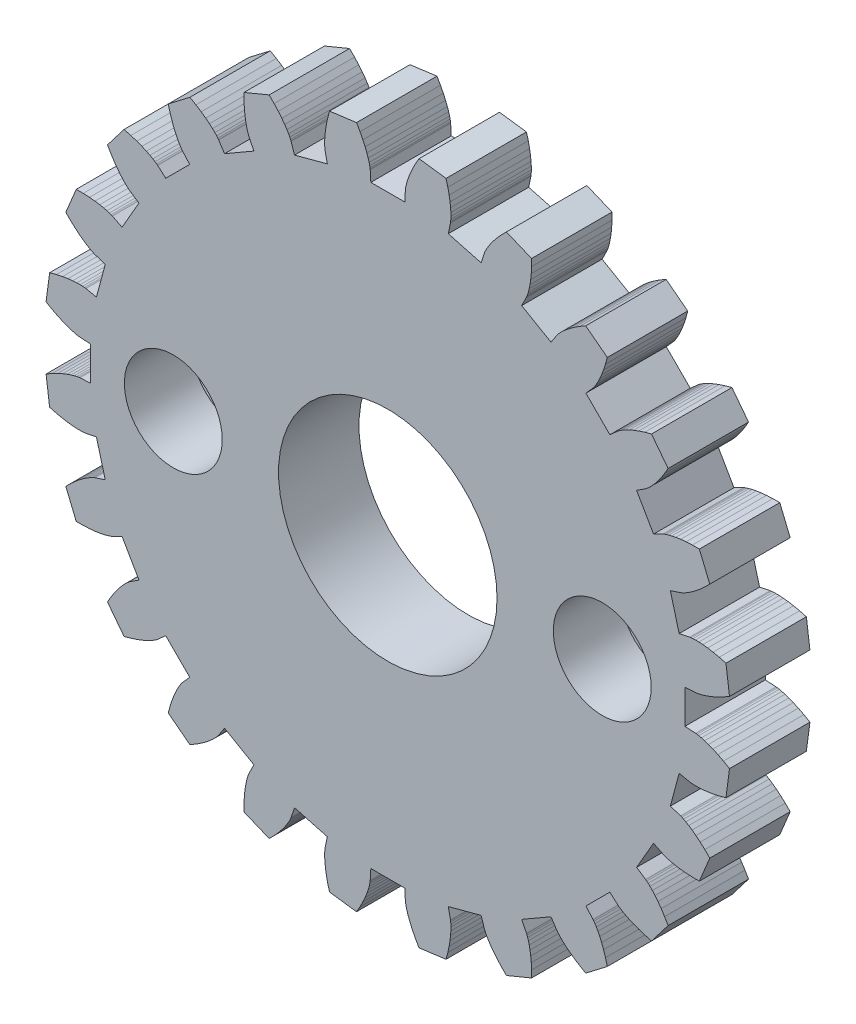
SolidWorks part; units mm, degrees
material "ABS"
ref_plane "Front Plane" through (0, 0, 0) normal (0, 0, 1) x (1, 0, 0)
ref_plane "Top Plane" through (0, 0, 0) normal (0, 1, 0) x (1, 0, 0)
ref_plane "Right Plane" through (0, 0, 0) normal (1, 0, 0) x (0, 0, -1)
sketch "Model" plane through (0, 0, 0) normal (0, 0, 1) x (1, 0, 0)
  line L0 (11.4813, -0.6559) -> (11.0819, -0.6331)
  line L1 (11.0819, -0.6331) -> (11.0819, 0.6331)
  line L2 (11.4813, 0.6559) -> (11.0819, 0.6331)
  line L3 (11.4813, 0.6559) -> (11.495, 0.6571)
  line L4 (11.495, 0.6571) -> (11.5358, 0.6626)
  line L5 (11.5358, 0.6626) -> (11.6033, 0.6749)
  line L6 (11.6033, 0.6749) -> (11.697, 0.6968)
  line L7 (11.697, 0.6968) -> (11.8158, 0.7307)
  line L8 (11.8158, 0.7307) -> (11.9589, 0.7792)
  line L9 (11.9589, 0.7792) -> (12.125, 0.8446)
  line L10 (12.125, 0.8446) -> (12.3128, 0.9294)
  line L11 (12.3128, 0.9294) -> (12.5206, 1.0358)
  line L12 (12.5206, 1.0358) -> (12.7468, 1.1658)
  line L13 (11.2598, 2.338) -> (11.2734, 2.3404)
  line L14 (11.2734, 2.3404) -> (11.3142, 2.3457)
  line L15 (11.3142, 2.3457) -> (11.3827, 2.3512)
  line L16 (11.3827, 2.3512) -> (11.4787, 2.3543)
  line L17 (11.4787, 2.3543) -> (11.6023, 2.3524)
  line L18 (11.6023, 2.3524) -> (11.7531, 2.3426)
  line L19 (11.7531, 2.3426) -> (11.9305, 2.3223)
  line L20 (11.9305, 2.3223) -> (12.1338, 2.289)
  line L21 (12.1338, 2.289) -> (12.362, 2.2401)
  line L22 (12.362, 2.2401) -> (12.6142, 2.173)
  line L23 (12.7468, 1.1658) -> (12.6142, 2.173)
  line L24 (11.2598, 2.338) -> (10.8682, 2.2567)
  line L25 (10.8682, 2.2567) -> (10.5405, 3.4797)
  line L26 (10.9203, 3.6051) -> (10.5405, 3.4797)
  line L27 (10.9203, 3.6051) -> (10.9332, 3.6098)
  line L28 (10.9332, 3.6098) -> (10.9712, 3.6257)
  line L29 (10.9712, 3.6257) -> (11.0333, 3.6551)
  line L30 (11.0333, 3.6551) -> (11.1181, 3.7004)
  line L31 (11.1181, 3.7004) -> (11.2241, 3.764)
  line L32 (11.2241, 3.764) -> (11.3497, 3.8478)
  line L33 (11.3497, 3.8478) -> (11.4933, 3.954)
  line L34 (11.4933, 3.954) -> (11.6527, 4.0845)
  line L35 (11.6527, 4.0845) -> (11.8259, 4.241)
  line L36 (11.8259, 4.241) -> (12.0107, 4.4252)
  line L37 (10.271, 5.1726) -> (10.2835, 5.1784)
  line L38 (10.2835, 5.1784) -> (10.3216, 5.1941)
  line L39 (10.3216, 5.1941) -> (10.3863, 5.2172)
  line L40 (10.3863, 5.2172) -> (10.4783, 5.245)
  line L41 (10.4783, 5.245) -> (10.5981, 5.2751)
  line L42 (10.5981, 5.2751) -> (10.7463, 5.3047)
  line L43 (10.7463, 5.3047) -> (10.9229, 5.331)
  line L44 (10.9229, 5.331) -> (11.1279, 5.3515)
  line L45 (11.1279, 5.3515) -> (11.361, 5.3633)
  line L46 (11.361, 5.3633) -> (11.622, 5.3638)
  line L47 (12.0107, 4.4252) -> (11.622, 5.3638)
  line L48 (10.271, 5.1726) -> (9.9138, 4.9927)
  line L49 (9.9138, 4.9927) -> (9.2807, 6.0892)
  line L50 (9.6151, 6.3087) -> (9.2807, 6.0892)
  line L51 (9.6151, 6.3087) -> (9.6264, 6.3166)
  line L52 (9.6264, 6.3166) -> (9.659, 6.3417)
  line L53 (9.659, 6.3417) -> (9.7113, 6.3862)
  line L54 (9.7113, 6.3862) -> (9.7815, 6.4519)
  line L55 (9.7815, 6.4519) -> (9.8675, 6.5407)
  line L56 (9.8675, 6.5407) -> (9.9671, 6.6542)
  line L57 (9.9671, 6.6542) -> (10.0783, 6.794)
  line L58 (10.0783, 6.794) -> (10.1985, 6.9613)
  line L59 (10.1985, 6.9613) -> (10.3253, 7.1573)
  line L60 (10.3253, 7.1573) -> (10.4561, 7.383)
  line L61 (8.5823, 7.6547) -> (8.5928, 7.6635)
  line L62 (8.5928, 7.6635) -> (8.6256, 7.6885)
  line L63 (8.6256, 7.6885) -> (8.6821, 7.7275)
  line L64 (8.6821, 7.7275) -> (8.7637, 7.7783)
  line L65 (8.7637, 7.7783) -> (8.8717, 7.8384)
  line L66 (8.8717, 7.8384) -> (9.0072, 7.9053)
  line L67 (9.0072, 7.9053) -> (9.1709, 7.9764)
  line L68 (9.1709, 7.9764) -> (9.3636, 8.0492)
  line L69 (9.3636, 8.0492) -> (9.5858, 8.121)
  line L70 (9.5858, 8.121) -> (9.8377, 8.189)
  line L71 (10.4561, 7.383) -> (9.8377, 8.189)
  line L72 (8.5823, 7.6547) -> (8.2838, 7.3885)
  line L73 (8.2838, 7.3885) -> (7.3885, 8.2838)
  line L74 (7.6547, 8.5823) -> (7.3885, 8.2838)
  line L75 (7.6547, 8.5823) -> (7.6635, 8.5928)
  line L76 (7.6635, 8.5928) -> (7.6885, 8.6256)
  line L77 (7.6885, 8.6256) -> (7.7275, 8.6821)
  line L78 (7.7275, 8.6821) -> (7.7783, 8.7637)
  line L79 (7.7783, 8.7637) -> (7.8384, 8.8717)
  line L80 (7.8384, 8.8717) -> (7.9053, 9.0072)
  line L81 (7.9053, 9.0072) -> (7.9764, 9.1709)
  line L82 (7.9764, 9.1709) -> (8.0492, 9.3636)
  line L83 (8.0492, 9.3636) -> (8.121, 9.5858)
  line L84 (8.121, 9.5858) -> (8.189, 9.8377)
  line L85 (6.3087, 9.6151) -> (6.3166, 9.6264)
  line L86 (6.3166, 9.6264) -> (6.3417, 9.659)
  line L87 (6.3417, 9.659) -> (6.3862, 9.7113)
  line L88 (6.3862, 9.7113) -> (6.4519, 9.7815)
  line L89 (6.4519, 9.7815) -> (6.5407, 9.8675)
  line L90 (6.5407, 9.8675) -> (6.6542, 9.9671)
  line L91 (6.6542, 9.9671) -> (6.794, 10.0783)
  line L92 (6.794, 10.0783) -> (6.9613, 10.1985)
  line L93 (6.9613, 10.1985) -> (7.1573, 10.3253)
  line L94 (7.1573, 10.3253) -> (7.383, 10.4561)
  line L95 (8.189, 9.8377) -> (7.383, 10.4561)
  line L96 (6.3087, 9.6151) -> (6.0892, 9.2807)
  line L97 (6.0892, 9.2807) -> (4.9927, 9.9138)
  line L98 (5.1726, 10.271) -> (4.9927, 9.9138)
  line L99 (5.1726, 10.271) -> (5.1784, 10.2835)
  line L100 (5.1784, 10.2835) -> (5.1941, 10.3216)
  line L101 (5.1941, 10.3216) -> (5.2172, 10.3863)
  line L102 (5.2172, 10.3863) -> (5.245, 10.4783)
  line L103 (5.245, 10.4783) -> (5.2751, 10.5981)
  line L104 (5.2751, 10.5981) -> (5.3047, 10.7463)
  line L105 (5.3047, 10.7463) -> (5.331, 10.9229)
  line L106 (5.331, 10.9229) -> (5.3515, 11.1279)
  line L107 (5.3515, 11.1279) -> (5.3633, 11.361)
  line L108 (5.3633, 11.361) -> (5.3638, 11.622)
  line L109 (3.6051, 10.9203) -> (3.6098, 10.9332)
  line L110 (3.6098, 10.9332) -> (3.6257, 10.9712)
  line L111 (3.6257, 10.9712) -> (3.6551, 11.0333)
  line L112 (3.6551, 11.0333) -> (3.7004, 11.1181)
  line L113 (3.7004, 11.1181) -> (3.764, 11.2241)
  line L114 (3.764, 11.2241) -> (3.8478, 11.3497)
  line L115 (3.8478, 11.3497) -> (3.954, 11.4933)
  line L116 (3.954, 11.4933) -> (4.0845, 11.6527)
  line L117 (4.0845, 11.6527) -> (4.241, 11.8259)
  line L118 (4.241, 11.8259) -> (4.4252, 12.0107)
  line L119 (5.3638, 11.622) -> (4.4252, 12.0107)
  line L120 (3.6051, 10.9203) -> (3.4797, 10.5405)
  line L121 (3.4797, 10.5405) -> (2.2567, 10.8682)
  line L122 (2.338, 11.2598) -> (2.2567, 10.8682)
  line L123 (2.338, 11.2598) -> (2.3404, 11.2734)
  line L124 (2.3404, 11.2734) -> (2.3457, 11.3142)
  line L125 (2.3457, 11.3142) -> (2.3512, 11.3827)
  line L126 (2.3512, 11.3827) -> (2.3543, 11.4787)
  line L127 (2.3543, 11.4787) -> (2.3524, 11.6023)
  line L128 (2.3524, 11.6023) -> (2.3426, 11.7531)
  line L129 (2.3426, 11.7531) -> (2.3223, 11.9305)
  line L130 (2.3223, 11.9305) -> (2.289, 12.1338)
  line L131 (2.289, 12.1338) -> (2.2401, 12.362)
  line L132 (2.2401, 12.362) -> (2.173, 12.6142)
  line L133 (0.6559, 11.4813) -> (0.6571, 11.495)
  line L134 (0.6571, 11.495) -> (0.6626, 11.5358)
  line L135 (0.6626, 11.5358) -> (0.6749, 11.6033)
  line L136 (0.6749, 11.6033) -> (0.6968, 11.697)
  line L137 (0.6968, 11.697) -> (0.7307, 11.8158)
  line L138 (0.7307, 11.8158) -> (0.7792, 11.9589)
  line L139 (0.7792, 11.9589) -> (0.8446, 12.125)
  line L140 (0.8446, 12.125) -> (0.9294, 12.3128)
  line L141 (0.9294, 12.3128) -> (1.0358, 12.5206)
  line L142 (1.0358, 12.5206) -> (1.1658, 12.7468)
  line L143 (2.173, 12.6142) -> (1.1658, 12.7468)
  line L144 (0.6559, 11.4813) -> (0.6331, 11.0819)
  line L145 (0.6331, 11.0819) -> (-0.6331, 11.0819)
  line L146 (-0.6559, 11.4813) -> (-0.6331, 11.0819)
  line L147 (-0.6559, 11.4813) -> (-0.6571, 11.495)
  line L148 (-0.6571, 11.495) -> (-0.6626, 11.5358)
  line L149 (-0.6626, 11.5358) -> (-0.6749, 11.6033)
  line L150 (-0.6749, 11.6033) -> (-0.6968, 11.697)
  line L151 (-0.6968, 11.697) -> (-0.7307, 11.8158)
  line L152 (-0.7307, 11.8158) -> (-0.7792, 11.9589)
  line L153 (-0.7792, 11.9589) -> (-0.8446, 12.125)
  line L154 (-0.8446, 12.125) -> (-0.9294, 12.3128)
  line L155 (-0.9294, 12.3128) -> (-1.0358, 12.5206)
  line L156 (-1.0358, 12.5206) -> (-1.1658, 12.7468)
  line L157 (-2.338, 11.2598) -> (-2.3404, 11.2734)
  line L158 (-2.3404, 11.2734) -> (-2.3457, 11.3142)
  line L159 (-2.3457, 11.3142) -> (-2.3512, 11.3827)
  line L160 (-2.3512, 11.3827) -> (-2.3543, 11.4787)
  line L161 (-2.3543, 11.4787) -> (-2.3524, 11.6023)
  line L162 (-2.3524, 11.6023) -> (-2.3426, 11.7531)
  line L163 (-2.3426, 11.7531) -> (-2.3223, 11.9305)
  line L164 (-2.3223, 11.9305) -> (-2.289, 12.1338)
  line L165 (-2.289, 12.1338) -> (-2.2401, 12.362)
  line L166 (-2.2401, 12.362) -> (-2.173, 12.6142)
  line L167 (-1.1658, 12.7468) -> (-2.173, 12.6142)
  line L168 (-2.338, 11.2598) -> (-2.2567, 10.8682)
  line L169 (-2.2567, 10.8682) -> (-3.4797, 10.5405)
  line L170 (-3.6051, 10.9203) -> (-3.4797, 10.5405)
  line L171 (-3.6051, 10.9203) -> (-3.6098, 10.9332)
  line L172 (-3.6098, 10.9332) -> (-3.6257, 10.9712)
  line L173 (-3.6257, 10.9712) -> (-3.6551, 11.0333)
  line L174 (-3.6551, 11.0333) -> (-3.7004, 11.1181)
  line L175 (-3.7004, 11.1181) -> (-3.764, 11.2241)
  line L176 (-3.764, 11.2241) -> (-3.8478, 11.3497)
  line L177 (-3.8478, 11.3497) -> (-3.954, 11.4933)
  line L178 (-3.954, 11.4933) -> (-4.0845, 11.6527)
  line L179 (-4.0845, 11.6527) -> (-4.241, 11.8259)
  line L180 (-4.241, 11.8259) -> (-4.4252, 12.0107)
  line L181 (-5.1726, 10.271) -> (-5.1784, 10.2835)
  line L182 (-5.1784, 10.2835) -> (-5.1941, 10.3216)
  line L183 (-5.1941, 10.3216) -> (-5.2172, 10.3863)
  line L184 (-5.2172, 10.3863) -> (-5.245, 10.4783)
  line L185 (-5.245, 10.4783) -> (-5.2751, 10.5981)
  line L186 (-5.2751, 10.5981) -> (-5.3047, 10.7463)
  line L187 (-5.3047, 10.7463) -> (-5.331, 10.9229)
  line L188 (-5.331, 10.9229) -> (-5.3515, 11.1279)
  line L189 (-5.3515, 11.1279) -> (-5.3633, 11.361)
  line L190 (-5.3633, 11.361) -> (-5.3638, 11.622)
  line L191 (-4.4252, 12.0107) -> (-5.3638, 11.622)
  line L192 (-5.1726, 10.271) -> (-4.9927, 9.9138)
  line L193 (-4.9927, 9.9138) -> (-6.0892, 9.2807)
  line L194 (-6.3087, 9.6151) -> (-6.0892, 9.2807)
  line L195 (-6.3087, 9.6151) -> (-6.3166, 9.6264)
  line L196 (-6.3166, 9.6264) -> (-6.3417, 9.659)
  line L197 (-6.3417, 9.659) -> (-6.3862, 9.7113)
  line L198 (-6.3862, 9.7113) -> (-6.4519, 9.7815)
  line L199 (-6.4519, 9.7815) -> (-6.5407, 9.8675)
  line L200 (-6.5407, 9.8675) -> (-6.6542, 9.9671)
  line L201 (-6.6542, 9.9671) -> (-6.794, 10.0783)
  line L202 (-6.794, 10.0783) -> (-6.9613, 10.1985)
  line L203 (-6.9613, 10.1985) -> (-7.1573, 10.3253)
  line L204 (-7.1573, 10.3253) -> (-7.383, 10.4561)
  line L205 (-7.6547, 8.5823) -> (-7.6635, 8.5928)
  line L206 (-7.6635, 8.5928) -> (-7.6885, 8.6256)
  line L207 (-7.6885, 8.6256) -> (-7.7275, 8.6821)
  line L208 (-7.7275, 8.6821) -> (-7.7783, 8.7637)
  line L209 (-7.7783, 8.7637) -> (-7.8384, 8.8717)
  line L210 (-7.8384, 8.8717) -> (-7.9053, 9.0072)
  line L211 (-7.9053, 9.0072) -> (-7.9764, 9.1709)
  line L212 (-7.9764, 9.1709) -> (-8.0492, 9.3636)
  line L213 (-8.0492, 9.3636) -> (-8.121, 9.5858)
  line L214 (-8.121, 9.5858) -> (-8.189, 9.8377)
  line L215 (-7.383, 10.4561) -> (-8.189, 9.8377)
  line L216 (-7.6547, 8.5823) -> (-7.3885, 8.2838)
  line L217 (-7.3885, 8.2838) -> (-8.2838, 7.3885)
  line L218 (-8.5823, 7.6547) -> (-8.2838, 7.3885)
  line L219 (-8.5823, 7.6547) -> (-8.5928, 7.6635)
  line L220 (-8.5928, 7.6635) -> (-8.6256, 7.6885)
  line L221 (-8.6256, 7.6885) -> (-8.6821, 7.7275)
  line L222 (-8.6821, 7.7275) -> (-8.7637, 7.7783)
  line L223 (-8.7637, 7.7783) -> (-8.8717, 7.8384)
  line L224 (-8.8717, 7.8384) -> (-9.0072, 7.9053)
  line L225 (-9.0072, 7.9053) -> (-9.1709, 7.9764)
  line L226 (-9.1709, 7.9764) -> (-9.3636, 8.0492)
  line L227 (-9.3636, 8.0492) -> (-9.5858, 8.121)
  line L228 (-9.5858, 8.121) -> (-9.8377, 8.189)
  line L229 (-9.6151, 6.3087) -> (-9.6264, 6.3166)
  line L230 (-9.6264, 6.3166) -> (-9.659, 6.3417)
  line L231 (-9.659, 6.3417) -> (-9.7113, 6.3862)
  line L232 (-9.7113, 6.3862) -> (-9.7815, 6.4519)
  line L233 (-9.7815, 6.4519) -> (-9.8675, 6.5407)
  line L234 (-9.8675, 6.5407) -> (-9.9671, 6.6542)
  line L235 (-9.9671, 6.6542) -> (-10.0783, 6.794)
  line L236 (-10.0783, 6.794) -> (-10.1985, 6.9613)
  line L237 (-10.1985, 6.9613) -> (-10.3253, 7.1573)
  line L238 (-10.3253, 7.1573) -> (-10.4561, 7.383)
  line L239 (-9.8377, 8.189) -> (-10.4561, 7.383)
  line L240 (-9.6151, 6.3087) -> (-9.2807, 6.0892)
  line L241 (-9.2807, 6.0892) -> (-9.9138, 4.9927)
  line L242 (-10.271, 5.1726) -> (-9.9138, 4.9927)
  line L243 (-10.271, 5.1726) -> (-10.2835, 5.1784)
  line L244 (-10.2835, 5.1784) -> (-10.3216, 5.1941)
  line L245 (-10.3216, 5.1941) -> (-10.3863, 5.2172)
  line L246 (-10.3863, 5.2172) -> (-10.4783, 5.245)
  line L247 (-10.4783, 5.245) -> (-10.5981, 5.2751)
  line L248 (-10.5981, 5.2751) -> (-10.7463, 5.3047)
  line L249 (-10.7463, 5.3047) -> (-10.9229, 5.331)
  line L250 (-10.9229, 5.331) -> (-11.1279, 5.3515)
  line L251 (-11.1279, 5.3515) -> (-11.361, 5.3633)
  line L252 (-11.361, 5.3633) -> (-11.622, 5.3638)
  line L253 (-10.9203, 3.6051) -> (-10.9332, 3.6098)
  line L254 (-10.9332, 3.6098) -> (-10.9712, 3.6257)
  line L255 (-10.9712, 3.6257) -> (-11.0333, 3.6551)
  line L256 (-11.0333, 3.6551) -> (-11.1181, 3.7004)
  line L257 (-11.1181, 3.7004) -> (-11.2241, 3.764)
  line L258 (-11.2241, 3.764) -> (-11.3497, 3.8478)
  line L259 (-11.3497, 3.8478) -> (-11.4933, 3.954)
  line L260 (-11.4933, 3.954) -> (-11.6527, 4.0845)
  line L261 (-11.6527, 4.0845) -> (-11.8259, 4.241)
  line L262 (-11.8259, 4.241) -> (-12.0107, 4.4252)
  line L263 (-11.622, 5.3638) -> (-12.0107, 4.4252)
  line L264 (-10.9203, 3.6051) -> (-10.5405, 3.4797)
  line L265 (-10.5405, 3.4797) -> (-10.8682, 2.2567)
  line L266 (-11.2598, 2.338) -> (-10.8682, 2.2567)
  line L267 (-11.2598, 2.338) -> (-11.2734, 2.3404)
  line L268 (-11.2734, 2.3404) -> (-11.3142, 2.3457)
  line L269 (-11.3142, 2.3457) -> (-11.3827, 2.3512)
  line L270 (-11.3827, 2.3512) -> (-11.4787, 2.3543)
  line L271 (-11.4787, 2.3543) -> (-11.6023, 2.3524)
  line L272 (-11.6023, 2.3524) -> (-11.7531, 2.3426)
  line L273 (-11.7531, 2.3426) -> (-11.9305, 2.3223)
  line L274 (-11.9305, 2.3223) -> (-12.1338, 2.289)
  line L275 (-12.1338, 2.289) -> (-12.362, 2.2401)
  line L276 (-12.362, 2.2401) -> (-12.6142, 2.173)
  line L277 (-11.4813, 0.6559) -> (-11.495, 0.6571)
  line L278 (-11.495, 0.6571) -> (-11.5358, 0.6626)
  line L279 (-11.5358, 0.6626) -> (-11.6033, 0.6749)
  line L280 (-11.6033, 0.6749) -> (-11.697, 0.6968)
  line L281 (-11.697, 0.6968) -> (-11.8158, 0.7307)
  line L282 (-11.8158, 0.7307) -> (-11.9589, 0.7792)
  line L283 (-11.9589, 0.7792) -> (-12.125, 0.8446)
  line L284 (-12.125, 0.8446) -> (-12.3128, 0.9294)
  line L285 (-12.3128, 0.9294) -> (-12.5206, 1.0358)
  line L286 (-12.5206, 1.0358) -> (-12.7468, 1.1658)
  line L287 (-12.6142, 2.173) -> (-12.7468, 1.1658)
  line L288 (-11.4813, 0.6559) -> (-11.0819, 0.6331)
  line L289 (-11.0819, 0.6331) -> (-11.0819, -0.6331)
  line L290 (-11.4813, -0.6559) -> (-11.0819, -0.6331)
  line L291 (-11.4813, -0.6559) -> (-11.495, -0.6571)
  line L292 (-11.495, -0.6571) -> (-11.5358, -0.6626)
  line L293 (-11.5358, -0.6626) -> (-11.6033, -0.6749)
  line L294 (-11.6033, -0.6749) -> (-11.697, -0.6968)
  line L295 (-11.697, -0.6968) -> (-11.8158, -0.7307)
  line L296 (-11.8158, -0.7307) -> (-11.9589, -0.7792)
  line L297 (-11.9589, -0.7792) -> (-12.125, -0.8446)
  line L298 (-12.125, -0.8446) -> (-12.3128, -0.9294)
  line L299 (-12.3128, -0.9294) -> (-12.5206, -1.0358)
  line L300 (-12.5206, -1.0358) -> (-12.7468, -1.1658)
  line L301 (-11.2598, -2.338) -> (-11.2734, -2.3404)
  line L302 (-11.2734, -2.3404) -> (-11.3142, -2.3457)
  line L303 (-11.3142, -2.3457) -> (-11.3827, -2.3512)
  line L304 (-11.3827, -2.3512) -> (-11.4787, -2.3543)
  line L305 (-11.4787, -2.3543) -> (-11.6023, -2.3524)
  line L306 (-11.6023, -2.3524) -> (-11.7531, -2.3426)
  line L307 (-11.7531, -2.3426) -> (-11.9305, -2.3223)
  line L308 (-11.9305, -2.3223) -> (-12.1338, -2.289)
  line L309 (-12.1338, -2.289) -> (-12.362, -2.2401)
  line L310 (-12.362, -2.2401) -> (-12.6142, -2.173)
  line L311 (-12.7468, -1.1658) -> (-12.6142, -2.173)
  line L312 (-11.2598, -2.338) -> (-10.8682, -2.2567)
  line L313 (-10.8682, -2.2567) -> (-10.5405, -3.4797)
  line L314 (-10.9203, -3.6051) -> (-10.5405, -3.4797)
  line L315 (-10.9203, -3.6051) -> (-10.9332, -3.6098)
  line L316 (-10.9332, -3.6098) -> (-10.9712, -3.6257)
  line L317 (-10.9712, -3.6257) -> (-11.0333, -3.6551)
  line L318 (-11.0333, -3.6551) -> (-11.1181, -3.7004)
  line L319 (-11.1181, -3.7004) -> (-11.2241, -3.764)
  line L320 (-11.2241, -3.764) -> (-11.3497, -3.8478)
  line L321 (-11.3497, -3.8478) -> (-11.4933, -3.954)
  line L322 (-11.4933, -3.954) -> (-11.6527, -4.0845)
  line L323 (-11.6527, -4.0845) -> (-11.8259, -4.241)
  line L324 (-11.8259, -4.241) -> (-12.0107, -4.4252)
  line L325 (-10.271, -5.1726) -> (-10.2835, -5.1784)
  line L326 (-10.2835, -5.1784) -> (-10.3216, -5.1941)
  line L327 (-10.3216, -5.1941) -> (-10.3863, -5.2172)
  line L328 (-10.3863, -5.2172) -> (-10.4783, -5.245)
  line L329 (-10.4783, -5.245) -> (-10.5981, -5.2751)
  line L330 (-10.5981, -5.2751) -> (-10.7463, -5.3047)
  line L331 (-10.7463, -5.3047) -> (-10.9229, -5.331)
  line L332 (-10.9229, -5.331) -> (-11.1279, -5.3515)
  line L333 (-11.1279, -5.3515) -> (-11.361, -5.3633)
  line L334 (-11.361, -5.3633) -> (-11.622, -5.3638)
  line L335 (-12.0107, -4.4252) -> (-11.622, -5.3638)
  line L336 (-10.271, -5.1726) -> (-9.9138, -4.9927)
  line L337 (-9.9138, -4.9927) -> (-9.2807, -6.0892)
  line L338 (-9.6151, -6.3087) -> (-9.2807, -6.0892)
  line L339 (-9.6151, -6.3087) -> (-9.6264, -6.3166)
  line L340 (-9.6264, -6.3166) -> (-9.659, -6.3417)
  line L341 (-9.659, -6.3417) -> (-9.7113, -6.3862)
  line L342 (-9.7113, -6.3862) -> (-9.7815, -6.4519)
  line L343 (-9.7815, -6.4519) -> (-9.8675, -6.5407)
  line L344 (-9.8675, -6.5407) -> (-9.9671, -6.6542)
  line L345 (-9.9671, -6.6542) -> (-10.0783, -6.794)
  line L346 (-10.0783, -6.794) -> (-10.1985, -6.9613)
  line L347 (-10.1985, -6.9613) -> (-10.3253, -7.1573)
  line L348 (-10.3253, -7.1573) -> (-10.4561, -7.383)
  line L349 (-8.5823, -7.6547) -> (-8.5928, -7.6635)
  line L350 (-8.5928, -7.6635) -> (-8.6256, -7.6885)
  line L351 (-8.6256, -7.6885) -> (-8.6821, -7.7275)
  line L352 (-8.6821, -7.7275) -> (-8.7637, -7.7783)
  line L353 (-8.7637, -7.7783) -> (-8.8717, -7.8384)
  line L354 (-8.8717, -7.8384) -> (-9.0072, -7.9053)
  line L355 (-9.0072, -7.9053) -> (-9.1709, -7.9764)
  line L356 (-9.1709, -7.9764) -> (-9.3636, -8.0492)
  line L357 (-9.3636, -8.0492) -> (-9.5858, -8.121)
  line L358 (-9.5858, -8.121) -> (-9.8377, -8.189)
  line L359 (-10.4561, -7.383) -> (-9.8377, -8.189)
  line L360 (-8.5823, -7.6547) -> (-8.2838, -7.3885)
  line L361 (-8.2838, -7.3885) -> (-7.3885, -8.2838)
  line L362 (-7.6547, -8.5823) -> (-7.3885, -8.2838)
  line L363 (-7.6547, -8.5823) -> (-7.6635, -8.5928)
  line L364 (-7.6635, -8.5928) -> (-7.6885, -8.6256)
  line L365 (-7.6885, -8.6256) -> (-7.7275, -8.6821)
  line L366 (-7.7275, -8.6821) -> (-7.7783, -8.7637)
  line L367 (-7.7783, -8.7637) -> (-7.8384, -8.8717)
  line L368 (-7.8384, -8.8717) -> (-7.9053, -9.0072)
  line L369 (-7.9053, -9.0072) -> (-7.9764, -9.1709)
  line L370 (-7.9764, -9.1709) -> (-8.0492, -9.3636)
  line L371 (-8.0492, -9.3636) -> (-8.121, -9.5858)
  line L372 (-8.121, -9.5858) -> (-8.189, -9.8377)
  line L373 (-6.3087, -9.6151) -> (-6.3166, -9.6264)
  line L374 (-6.3166, -9.6264) -> (-6.3417, -9.659)
  line L375 (-6.3417, -9.659) -> (-6.3862, -9.7113)
  line L376 (-6.3862, -9.7113) -> (-6.4519, -9.7815)
  line L377 (-6.4519, -9.7815) -> (-6.5407, -9.8675)
  line L378 (-6.5407, -9.8675) -> (-6.6542, -9.9671)
  line L379 (-6.6542, -9.9671) -> (-6.794, -10.0783)
  line L380 (-6.794, -10.0783) -> (-6.9613, -10.1985)
  line L381 (-6.9613, -10.1985) -> (-7.1573, -10.3253)
  line L382 (-7.1573, -10.3253) -> (-7.383, -10.4561)
  line L383 (-8.189, -9.8377) -> (-7.383, -10.4561)
  line L384 (-6.3087, -9.6151) -> (-6.0892, -9.2807)
  line L385 (-6.0892, -9.2807) -> (-4.9927, -9.9138)
  line L386 (-5.1726, -10.271) -> (-4.9927, -9.9138)
  line L387 (-5.1726, -10.271) -> (-5.1784, -10.2835)
  line L388 (-5.1784, -10.2835) -> (-5.1941, -10.3216)
  line L389 (-5.1941, -10.3216) -> (-5.2172, -10.3863)
  line L390 (-5.2172, -10.3863) -> (-5.245, -10.4783)
  line L391 (-5.245, -10.4783) -> (-5.2751, -10.5981)
  line L392 (-5.2751, -10.5981) -> (-5.3047, -10.7463)
  line L393 (-5.3047, -10.7463) -> (-5.331, -10.9229)
  line L394 (-5.331, -10.9229) -> (-5.3515, -11.1279)
  line L395 (-5.3515, -11.1279) -> (-5.3633, -11.361)
  line L396 (-5.3633, -11.361) -> (-5.3638, -11.622)
  line L397 (-3.6051, -10.9203) -> (-3.6098, -10.9332)
  line L398 (-3.6098, -10.9332) -> (-3.6257, -10.9712)
  line L399 (-3.6257, -10.9712) -> (-3.6551, -11.0333)
  line L400 (-3.6551, -11.0333) -> (-3.7004, -11.1181)
  line L401 (-3.7004, -11.1181) -> (-3.764, -11.2241)
  line L402 (-3.764, -11.2241) -> (-3.8478, -11.3497)
  line L403 (-3.8478, -11.3497) -> (-3.954, -11.4933)
  line L404 (-3.954, -11.4933) -> (-4.0845, -11.6527)
  line L405 (-4.0845, -11.6527) -> (-4.241, -11.8259)
  line L406 (-4.241, -11.8259) -> (-4.4252, -12.0107)
  line L407 (-5.3638, -11.622) -> (-4.4252, -12.0107)
  line L408 (-3.6051, -10.9203) -> (-3.4797, -10.5405)
  line L409 (-3.4797, -10.5405) -> (-2.2567, -10.8682)
  line L410 (-2.338, -11.2598) -> (-2.2567, -10.8682)
  line L411 (-2.338, -11.2598) -> (-2.3404, -11.2734)
  line L412 (-2.3404, -11.2734) -> (-2.3457, -11.3142)
  line L413 (-2.3457, -11.3142) -> (-2.3512, -11.3827)
  line L414 (-2.3512, -11.3827) -> (-2.3543, -11.4787)
  line L415 (-2.3543, -11.4787) -> (-2.3524, -11.6023)
  line L416 (-2.3524, -11.6023) -> (-2.3426, -11.7531)
  line L417 (-2.3426, -11.7531) -> (-2.3223, -11.9305)
  line L418 (-2.3223, -11.9305) -> (-2.289, -12.1338)
  line L419 (-2.289, -12.1338) -> (-2.2401, -12.362)
  line L420 (-2.2401, -12.362) -> (-2.173, -12.6142)
  line L421 (-0.6559, -11.4813) -> (-0.6571, -11.495)
  line L422 (-0.6571, -11.495) -> (-0.6626, -11.5358)
  line L423 (-0.6626, -11.5358) -> (-0.6749, -11.6033)
  line L424 (-0.6749, -11.6033) -> (-0.6968, -11.697)
  line L425 (-0.6968, -11.697) -> (-0.7307, -11.8158)
  line L426 (-0.7307, -11.8158) -> (-0.7792, -11.9589)
  line L427 (-0.7792, -11.9589) -> (-0.8446, -12.125)
  line L428 (-0.8446, -12.125) -> (-0.9294, -12.3128)
  line L429 (-0.9294, -12.3128) -> (-1.0358, -12.5206)
  line L430 (-1.0358, -12.5206) -> (-1.1658, -12.7468)
  line L431 (-2.173, -12.6142) -> (-1.1658, -12.7468)
  line L432 (-0.6559, -11.4813) -> (-0.6331, -11.0819)
  line L433 (-0.6331, -11.0819) -> (0.6331, -11.0819)
  line L434 (0.6559, -11.4813) -> (0.6331, -11.0819)
  line L435 (0.6559, -11.4813) -> (0.6571, -11.495)
  line L436 (0.6571, -11.495) -> (0.6626, -11.5358)
  line L437 (0.6626, -11.5358) -> (0.6749, -11.6033)
  line L438 (0.6749, -11.6033) -> (0.6968, -11.697)
  line L439 (0.6968, -11.697) -> (0.7307, -11.8158)
  line L440 (0.7307, -11.8158) -> (0.7792, -11.9589)
  line L441 (0.7792, -11.9589) -> (0.8446, -12.125)
  line L442 (0.8446, -12.125) -> (0.9294, -12.3128)
  line L443 (0.9294, -12.3128) -> (1.0358, -12.5206)
  line L444 (1.0358, -12.5206) -> (1.1658, -12.7468)
  line L445 (2.338, -11.2598) -> (2.3404, -11.2734)
  line L446 (2.3404, -11.2734) -> (2.3457, -11.3142)
  line L447 (2.3457, -11.3142) -> (2.3512, -11.3827)
  line L448 (2.3512, -11.3827) -> (2.3543, -11.4787)
  line L449 (2.3543, -11.4787) -> (2.3524, -11.6023)
  line L450 (2.3524, -11.6023) -> (2.3426, -11.7531)
  line L451 (2.3426, -11.7531) -> (2.3223, -11.9305)
  line L452 (2.3223, -11.9305) -> (2.289, -12.1338)
  line L453 (2.289, -12.1338) -> (2.2401, -12.362)
  line L454 (2.2401, -12.362) -> (2.173, -12.6142)
  line L455 (1.1658, -12.7468) -> (2.173, -12.6142)
  line L456 (2.338, -11.2598) -> (2.2567, -10.8682)
  line L457 (2.2567, -10.8682) -> (3.4797, -10.5405)
  line L458 (3.6051, -10.9203) -> (3.4797, -10.5405)
  line L459 (3.6051, -10.9203) -> (3.6098, -10.9332)
  line L460 (3.6098, -10.9332) -> (3.6257, -10.9712)
  line L461 (3.6257, -10.9712) -> (3.6551, -11.0333)
  line L462 (3.6551, -11.0333) -> (3.7004, -11.1181)
  line L463 (3.7004, -11.1181) -> (3.764, -11.2241)
  line L464 (3.764, -11.2241) -> (3.8478, -11.3497)
  line L465 (3.8478, -11.3497) -> (3.954, -11.4933)
  line L466 (3.954, -11.4933) -> (4.0845, -11.6527)
  line L467 (4.0845, -11.6527) -> (4.241, -11.8259)
  line L468 (4.241, -11.8259) -> (4.4252, -12.0107)
  line L469 (5.1726, -10.271) -> (5.1784, -10.2835)
  line L470 (5.1784, -10.2835) -> (5.1941, -10.3216)
  line L471 (5.1941, -10.3216) -> (5.2172, -10.3863)
  line L472 (5.2172, -10.3863) -> (5.245, -10.4783)
  line L473 (5.245, -10.4783) -> (5.2751, -10.5981)
  line L474 (5.2751, -10.5981) -> (5.3047, -10.7463)
  line L475 (5.3047, -10.7463) -> (5.331, -10.9229)
  line L476 (5.331, -10.9229) -> (5.3515, -11.1279)
  line L477 (5.3515, -11.1279) -> (5.3633, -11.361)
  line L478 (5.3633, -11.361) -> (5.3638, -11.622)
  line L479 (4.4252, -12.0107) -> (5.3638, -11.622)
  line L480 (5.1726, -10.271) -> (4.9927, -9.9138)
  line L481 (4.9927, -9.9138) -> (6.0892, -9.2807)
  line L482 (6.3087, -9.6151) -> (6.0892, -9.2807)
  line L483 (6.3087, -9.6151) -> (6.3166, -9.6264)
  line L484 (6.3166, -9.6264) -> (6.3417, -9.659)
  line L485 (6.3417, -9.659) -> (6.3862, -9.7113)
  line L486 (6.3862, -9.7113) -> (6.4519, -9.7815)
  line L487 (6.4519, -9.7815) -> (6.5407, -9.8675)
  line L488 (6.5407, -9.8675) -> (6.6542, -9.9671)
  line L489 (6.6542, -9.9671) -> (6.794, -10.0783)
  line L490 (6.794, -10.0783) -> (6.9613, -10.1985)
  line L491 (6.9613, -10.1985) -> (7.1573, -10.3253)
  line L492 (7.1573, -10.3253) -> (7.383, -10.4561)
  line L493 (7.6547, -8.5823) -> (7.6635, -8.5928)
  line L494 (7.6635, -8.5928) -> (7.6885, -8.6256)
  line L495 (7.6885, -8.6256) -> (7.7275, -8.6821)
  line L496 (7.7275, -8.6821) -> (7.7783, -8.7637)
  line L497 (7.7783, -8.7637) -> (7.8384, -8.8717)
  line L498 (7.8384, -8.8717) -> (7.9053, -9.0072)
  line L499 (7.9053, -9.0072) -> (7.9764, -9.1709)
  line L500 (7.9764, -9.1709) -> (8.0492, -9.3636)
  line L501 (8.0492, -9.3636) -> (8.121, -9.5858)
  line L502 (8.121, -9.5858) -> (8.189, -9.8377)
  line L503 (7.383, -10.4561) -> (8.189, -9.8377)
  line L504 (7.6547, -8.5823) -> (7.3885, -8.2838)
  line L505 (7.3885, -8.2838) -> (8.2838, -7.3885)
  line L506 (8.5823, -7.6547) -> (8.2838, -7.3885)
  line L507 (8.5823, -7.6547) -> (8.5928, -7.6635)
  line L508 (8.5928, -7.6635) -> (8.6256, -7.6885)
  line L509 (8.6256, -7.6885) -> (8.6821, -7.7275)
  line L510 (8.6821, -7.7275) -> (8.7637, -7.7783)
  line L511 (8.7637, -7.7783) -> (8.8717, -7.8384)
  line L512 (8.8717, -7.8384) -> (9.0072, -7.9053)
  line L513 (9.0072, -7.9053) -> (9.1709, -7.9764)
  line L514 (9.1709, -7.9764) -> (9.3636, -8.0492)
  line L515 (9.3636, -8.0492) -> (9.5858, -8.121)
  line L516 (9.5858, -8.121) -> (9.8377, -8.189)
  line L517 (9.6151, -6.3087) -> (9.6264, -6.3166)
  line L518 (9.6264, -6.3166) -> (9.659, -6.3417)
  line L519 (9.659, -6.3417) -> (9.7113, -6.3862)
  line L520 (9.7113, -6.3862) -> (9.7815, -6.4519)
  line L521 (9.7815, -6.4519) -> (9.8675, -6.5407)
  line L522 (9.8675, -6.5407) -> (9.9671, -6.6542)
  line L523 (9.9671, -6.6542) -> (10.0783, -6.794)
  line L524 (10.0783, -6.794) -> (10.1985, -6.9613)
  line L525 (10.1985, -6.9613) -> (10.3253, -7.1573)
  line L526 (10.3253, -7.1573) -> (10.4561, -7.383)
  line L527 (9.8377, -8.189) -> (10.4561, -7.383)
  line L528 (9.6151, -6.3087) -> (9.2807, -6.0892)
  line L529 (9.2807, -6.0892) -> (9.9138, -4.9927)
  line L530 (10.271, -5.1726) -> (9.9138, -4.9927)
  line L531 (10.271, -5.1726) -> (10.2835, -5.1784)
  line L532 (10.2835, -5.1784) -> (10.3216, -5.1941)
  line L533 (10.3216, -5.1941) -> (10.3863, -5.2172)
  line L534 (10.3863, -5.2172) -> (10.4783, -5.245)
  line L535 (10.4783, -5.245) -> (10.5981, -5.2751)
  line L536 (10.5981, -5.2751) -> (10.7463, -5.3047)
  line L537 (10.7463, -5.3047) -> (10.9229, -5.331)
  line L538 (10.9229, -5.331) -> (11.1279, -5.3515)
  line L539 (11.1279, -5.3515) -> (11.361, -5.3633)
  line L540 (11.361, -5.3633) -> (11.622, -5.3638)
  line L541 (10.9203, -3.6051) -> (10.9332, -3.6098)
  line L542 (10.9332, -3.6098) -> (10.9712, -3.6257)
  line L543 (10.9712, -3.6257) -> (11.0333, -3.6551)
  line L544 (11.0333, -3.6551) -> (11.1181, -3.7004)
  line L545 (11.1181, -3.7004) -> (11.2241, -3.764)
  line L546 (11.2241, -3.764) -> (11.3497, -3.8478)
  line L547 (11.3497, -3.8478) -> (11.4933, -3.954)
  line L548 (11.4933, -3.954) -> (11.6527, -4.0845)
  line L549 (11.6527, -4.0845) -> (11.8259, -4.241)
  line L550 (11.8259, -4.241) -> (12.0107, -4.4252)
  line L551 (11.622, -5.3638) -> (12.0107, -4.4252)
  line L552 (10.9203, -3.6051) -> (10.5405, -3.4797)
  line L553 (10.5405, -3.4797) -> (10.8682, -2.2567)
  line L554 (11.2598, -2.338) -> (10.8682, -2.2567)
  line L555 (11.2598, -2.338) -> (11.2734, -2.3404)
  line L556 (11.2734, -2.3404) -> (11.3142, -2.3457)
  line L557 (11.3142, -2.3457) -> (11.3827, -2.3512)
  line L558 (11.3827, -2.3512) -> (11.4787, -2.3543)
  line L559 (11.4787, -2.3543) -> (11.6023, -2.3524)
  line L560 (11.6023, -2.3524) -> (11.7531, -2.3426)
  line L561 (11.7531, -2.3426) -> (11.9305, -2.3223)
  line L562 (11.9305, -2.3223) -> (12.1338, -2.289)
  line L563 (12.1338, -2.289) -> (12.362, -2.2401)
  line L564 (12.362, -2.2401) -> (12.6142, -2.173)
  line L565 (11.4813, -0.6559) -> (11.495, -0.6571)
  line L566 (11.495, -0.6571) -> (11.5358, -0.6626)
  line L567 (11.5358, -0.6626) -> (11.6033, -0.6749)
  line L568 (11.6033, -0.6749) -> (11.697, -0.6968)
  line L569 (11.697, -0.6968) -> (11.8158, -0.7307)
  line L570 (11.8158, -0.7307) -> (11.9589, -0.7792)
  line L571 (11.9589, -0.7792) -> (12.125, -0.8446)
  line L572 (12.125, -0.8446) -> (12.3128, -0.9294)
  line L573 (12.3128, -0.9294) -> (12.5206, -1.0358)
  line L574 (12.5206, -1.0358) -> (12.7468, -1.1658)
  line L575 (12.6142, -2.173) -> (12.7468, -1.1658)
extrude "Main Gear Body" add sketch "Model" along normal blind 3
sketch "Sketch1" plane through (0, 0, 3) normal (0, 0, 1) x (1, 0, 0)
  line L0 (-8, 0) -> (8, 0) construction
  circle A0 centre (0, 0) radius 4.075
  circle A1 centre (-8, 0) radius 1.15
  circle A2 centre (8, 0) radius 1.15
  dimension "D2" = 2.3
  dimension "D3" = 8.15
  dimension "D1" = 16
extrude "Servo Clearance" cut sketch "Sketch1" against normal through all
sketch "Sketch2" plane through (0, 0, 3) normal (0, 0, 1) x (1, 0, 0)
  circle A0 centre (8, 0) radius 1.825
  circle A1 centre (-8, 0) radius 1.825
  circle A3 centre (-8, 0) radius 1.15 construction
  circle A4 centre (8, 0) radius 1.15 construction
  dimension "D1" = 3.65
extrude "Bolt Head Clearance" cut sketch "Sketch2" against normal blind 2.5
ref_point "Point1"
equation "\"D3@Sketch1\"=8+\"print fit@values@params_print.sldprt\""
equation "\"D1@Sketch2\"=3.5+\"print fit@values@params_print.sldprt\""
